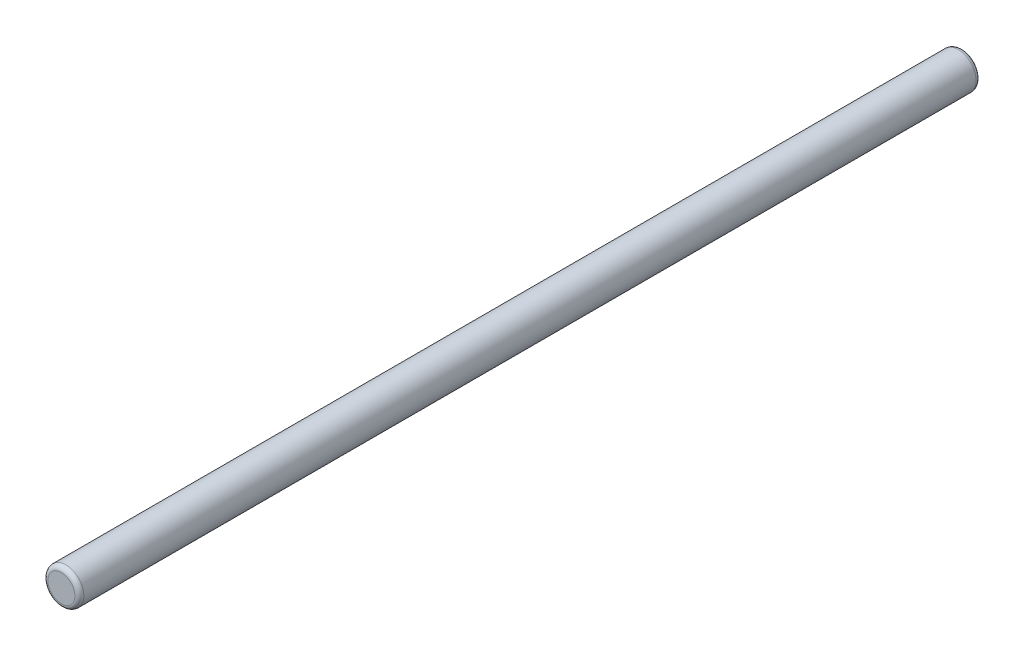
SolidWorks part; units mm, degrees
ref_plane "Ebene vorne" through (0, 0, 0) normal (0, 0, 1) x (1, 0, 0)
ref_plane "Ebene oben" through (0, 0, 0) normal (0, 1, 0) x (1, 0, 0)
ref_plane "Ebene rechts" through (0, 0, 0) normal (1, 0, 0) x (0, 0, -1)
sketch "Skizze1" plane through (0, 0, 0) normal (0, 0, 1) x (1, 0, 0)
  circle A0 centre (0, 0) radius 4
  dimension "D1" = 8
extrude "Aufsatz-Linear austragen1" add sketch "Skizze1" along normal blind 200
fillet "Verrundung1" radius 1 2 edges at (4, 0, 200) (4, 0, 0)
